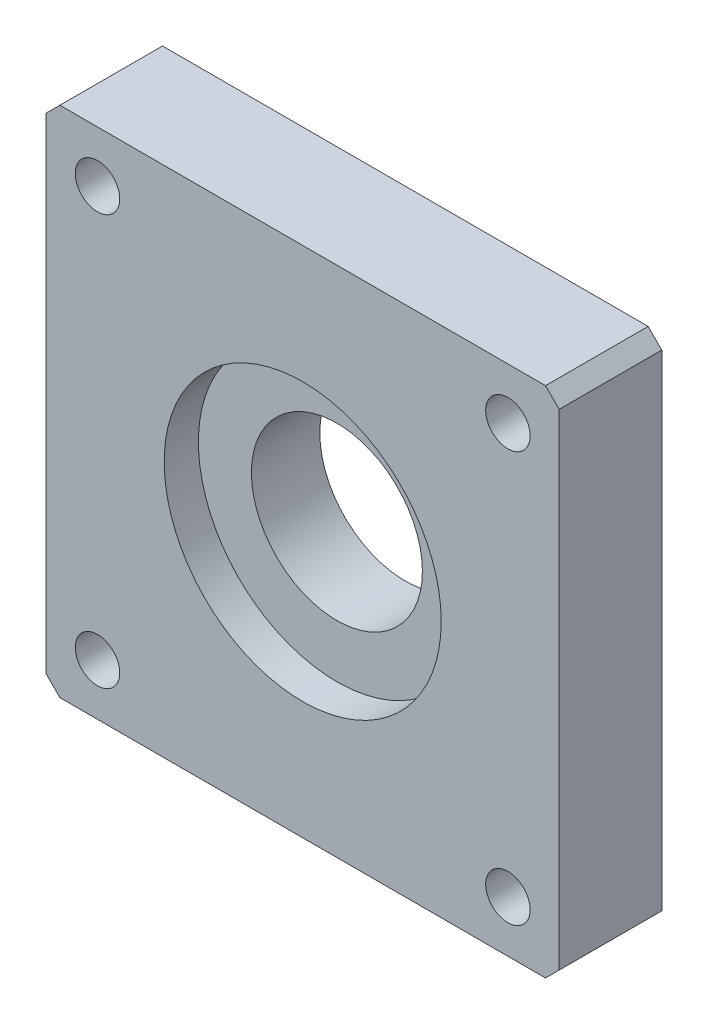
SolidWorks part; units mm, degrees
ref_plane "前视基准面" through (0, 0, 0) normal (0, 0, 1) x (1, 0, 0)
ref_plane "上视基准面" through (0, 0, 0) normal (0, 1, 0) x (1, 0, 0)
ref_plane "右视基准面" through (0, 0, 0) normal (1, 0, 0) x (0, 0, -1)
other "Configuration Table"
sketch "草图1" plane through (0, 0, 0) normal (0, 0, 1) x (1, 0, 0)
  line L1 (0, 0) -> (75, 0)
  line L2 (0, 0) -> (0, -75)
  line L3 (0, -75) -> (75, -75)
  line L4 (75, 0) -> (75, -75)
  dimension "D1" = 75
  dimension "D2" = 75
extrude "凸台-拉伸1" add sketch "草图1" along normal blind 15
chamfer "倒角1" distance 2 angle 45 4 edges at (75, -75, 7.5) (75, 0, 7.5) (0, -75, 7.5) (0, 0, 7.5)
sketch "草图2" plane through (0, 0, 15) normal (0, 0, 1) x (1, 0, 0)
  line L0 (0, -37.5) -> (75, -37.5) construction
  line L1 (0, -2) -> (0, -73) construction
  line L2 (75, -73) -> (75, -2) construction
  line L3 (37.5, 0) -> (37.5, -75) construction
  line L4 (73, 0) -> (2, 0) construction
  line L5 (2, -75) -> (73, -75) construction
  circle A0 centre (37.5, -37.5) radius 12.5
  circle A1 centre (7.5, -7.5) radius 3.25
  circle A2 centre (67.5, -7.5) radius 3.25
  circle A3 centre (67.5, -67.5) radius 3.25
  circle A4 centre (7.5, -67.5) radius 3.25
  dimension "D1" = 25
  dimension "D2" = 6.5
  dimension "D3" = 7.5
  dimension "D4" = 7.5
extrude "切除-拉伸1" cut sketch "草图2" against normal through all
sketch "草图3" plane through (0, 0, 15) normal (0, 0, 1) x (1, 0, 0)
  circle A0 centre (37.5, -37.5) radius 20.25
  dimension "D1" = 40.5
extrude "切除-拉伸2" cut sketch "草图3" against normal blind 5
